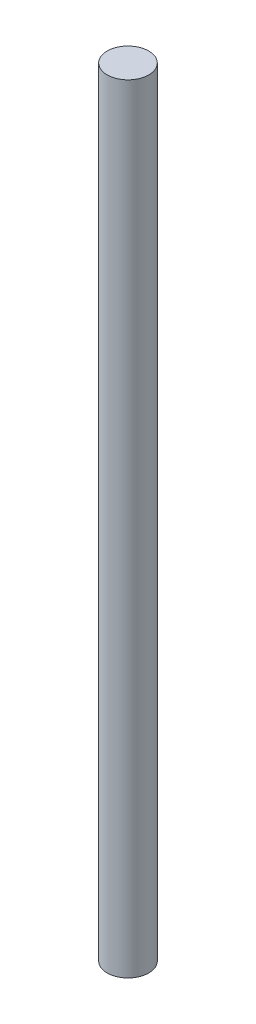
SolidWorks part; units mm, degrees
ref_plane "Ön Düzlem" through (0, 0, 0) normal (0, 0, 1) x (1, 0, 0)
ref_plane "Üst Düzlem" through (0, 0, 0) normal (0, 1, 0) x (1, 0, 0)
ref_plane "Sağ Düzlem" through (0, 0, 0) normal (1, 0, 0) x (0, 0, -1)
sketch "Çizim1" plane through (0, 0, 0) normal (0, 1, 0) x (1, 0, 0)
  circle A0 centre (0, 0) radius 8
  dimension "D1" = 16
extrude "Yükseklik-Ekstrüzyon1" add sketch "Çizim1" along normal blind 300
